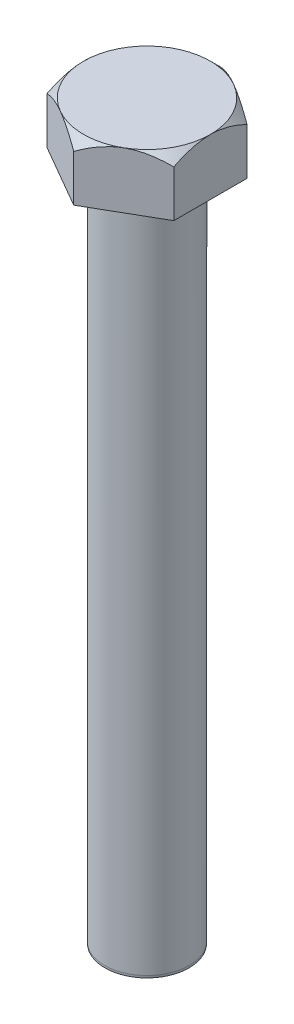
SolidWorks part; units mm, degrees
ref_plane "Front Plane" through (0, 0, 0) normal (0, 0, 1) x (1, 0, 0)
ref_plane "Top Plane" through (0, 0, 0) normal (0, 1, 0) x (1, 0, 0)
ref_plane "Right Plane" through (0, 0, 0) normal (1, 0, 0) x (0, 0, -1)
sketch "Sketch1" plane through (0, 0, 0) normal (0, 1, 0) x (1, 0, 0)
  line L1 (0, 8.2562) -> (-7.1501, 4.1281)
  line L2 (-7.1501, 4.1281) -> (-7.1501, -4.1281)
  line L3 (-7.1501, -4.1281) -> (0, -8.2562)
  line L4 (0, -8.2562) -> (7.1501, -4.1281)
  line L5 (7.1501, -4.1281) -> (7.1501, 4.1281)
  line L6 (7.1501, 4.1281) -> (0, 8.2562)
  circle A0 centre (0, 0) radius 7.1501 construction
  dimension "D1" = 14.3002
extrude "Boss-Extrude1" add sketch "Sketch1" along normal blind 6.35
sketch "Sketch2" plane through (0, 0, 0) normal (0, -1, 0) x (1, 0, 0)
  circle A0 centre (0, 0) radius 4.7625
  dimension "D1" = 9.525
extrude "Boss-Extrude2" add sketch "Sketch2" along normal blind 76.2
cosmetic thread "Cosmetic Thread1" parameters "D2"=8.2652
sketch "Sketch3" plane through (0, 6.35, 0) normal (0, 1, 0) x (1, 0, 0)
  circle A0 centre (0, 0) radius 7.1501
extrude "Cut-Extrude1" cut sketch "Sketch3" against normal blind 20.32 draft 45 flip side to cut
chamfer "Chamfer1" distance 0.254 angle 5 1 edges at (0, -76.2, -4.7625)
